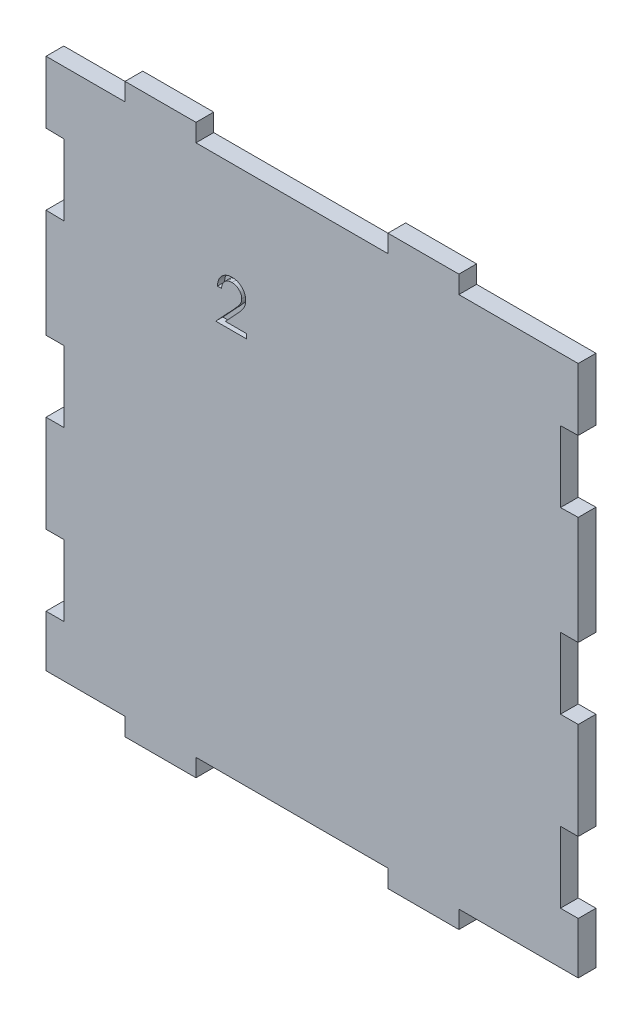
SolidWorks part; units mm, degrees
ref_plane "Front Plane" through (0, 0, 0) normal (0, 0, 1) x (1, 0, 0)
ref_plane "Top Plane" through (0, 0, 0) normal (0, 1, 0) x (1, 0, 0)
ref_plane "Right Plane" through (0, 0, 0) normal (1, 0, 0) x (0, 0, -1)
sketch "Sketch1" plane through (0, 0, 0) normal (0, 0, 1) x (1, 0, 0)
  line L0 (-73.6451, -74.8645) -> (-51.3839, -74.8645)
  line L1 (-73.6451, -74.8645) -> (-73.6451, -60.3287)
  line L2 (-73.6451, 75.1355) -> (-51.3839, 75.1355)
  line L3 (76.3549, -74.8645) -> (76.3549, -60.3287)
  line L4 (-73.6451, -74.8645) -> (76.3549, 75.1355) construction
  line L5 (-73.6451, 75.1355) -> (76.3549, -74.8645) construction
  line L6 (-51.3839, 80.1355) -> (-51.3839, 75.1355)
  line L7 (-31.3839, 80.1355) -> (-31.3839, 75.1355)
  line L9 (22.7158, 80.1355) -> (22.7158, 75.1355)
  line L10 (42.7158, 80.1355) -> (42.7158, 75.1355)
  line L12 (-73.6451, 57.5712) -> (-68.6461, 57.4708)
  line L13 (-73.6451, 37.5712) -> (-68.6461, 37.4708)
  line L14 (-68.6461, 57.4708) -> (-68.6461, 37.4708)
  line L15 (-73.6451, 7.0264) -> (-68.6451, 7.0264)
  line L16 (-73.6451, -12.9736) -> (-68.6451, -12.9736)
  line L17 (-68.6451, 7.0264) -> (-68.6451, -12.9736)
  line L18 (-73.6451, -40.3287) -> (-68.6451, -40.3287)
  line L19 (-68.6451, -40.3287) -> (-68.6451, -60.3287)
  line L20 (-73.6451, -60.3287) -> (-68.6451, -60.3287)
  line L21 (-68.6451, 0.1355) -> (71.3549, 0.1355) construction
  line L22 (1.3549, 75.1355) -> (1.3549, -74.8645) construction
  line L23 (42.7158, -79.8645) -> (42.7158, -74.8645)
  line L24 (22.7158, -79.8645) -> (22.7158, -74.8645)
  line L26 (-31.3839, -79.8645) -> (-31.3839, -74.8645)
  line L27 (-51.3839, -79.8645) -> (-51.3839, -74.8645)
  line L29 (76.3549, -60.3287) -> (71.3549, -60.3287)
  line L30 (71.3549, -40.3287) -> (71.3549, -60.3287)
  line L31 (76.3549, -40.3287) -> (71.3549, -40.3287)
  line L32 (76.3549, -12.9736) -> (71.3549, -12.9736)
  line L33 (71.3549, 7.0264) -> (71.3549, -12.9736)
  line L34 (76.3549, 7.0264) -> (71.3549, 7.0264)
  line L35 (76.3549, 37.5712) -> (71.3559, 37.4708)
  line L36 (71.3559, 57.4708) -> (71.3559, 37.4708)
  line L37 (76.3549, 57.5712) -> (71.3559, 57.4708)
  line L38 (-31.3839, 75.1355) -> (22.7158, 75.1355)
  line L39 (42.7158, 75.1355) -> (76.3549, 75.1355)
  line L40 (76.3549, 57.5712) -> (76.3549, 75.1355)
  line L41 (76.3549, 7.0264) -> (76.3549, 37.5712)
  line L42 (76.3549, -40.3287) -> (76.3549, -12.9736)
  line L43 (42.7158, -74.8645) -> (76.3549, -74.8645)
  line L44 (-31.3839, -74.8645) -> (22.7158, -74.8645)
  line L45 (-73.6451, -40.3287) -> (-73.6451, -12.9736)
  line L46 (-73.6451, 7.0264) -> (-73.6451, 37.5712)
  line L47 (-73.6451, 57.5712) -> (-73.6451, 75.1355)
  line L48 (-73.6451, 75.1355) -> (76.3549, 75.1355) construction
  line L49 (-73.6451, -74.8645) -> (76.3549, -74.8645) construction
  line L50 (22.7158, 80.1355) -> (42.7158, 80.1355)
  line L51 (-51.3839, 80.1355) -> (-31.3839, 80.1355)
  line L52 (-73.6451, 225.1355) -> (76.3549, 225.1355) construction
  line L53 (22.7158, -79.8645) -> (42.7158, -79.8645)
  line L54 (-51.3839, -79.8645) -> (-31.3839, -79.8645)
  point P0 (1.3549, 0.1355)
  dimension "D1" = 150
  dimension "D2" = 150
  dimension "D7" = 5
  dimension "D8" = 5
  dimension "D9" = 5
  dimension "D10" = 20
  dimension "D11" = 20
  dimension "D12" = 20
  dimension "D13" = 5
  dimension "D14" = 5
  dimension "D15" = 5
extrude "Boss-Extrude1" add sketch "Sketch1" along normal blind 5
sketch "Sketch2" plane through (0, 0, 5) normal (0, 0, 1) x (1, 0, 0)
  text T0 "2\r\n" font "Century Gothic" height in points 48
extrude "Cut-Extrude1" cut sketch "Sketch2" against normal blind 2
